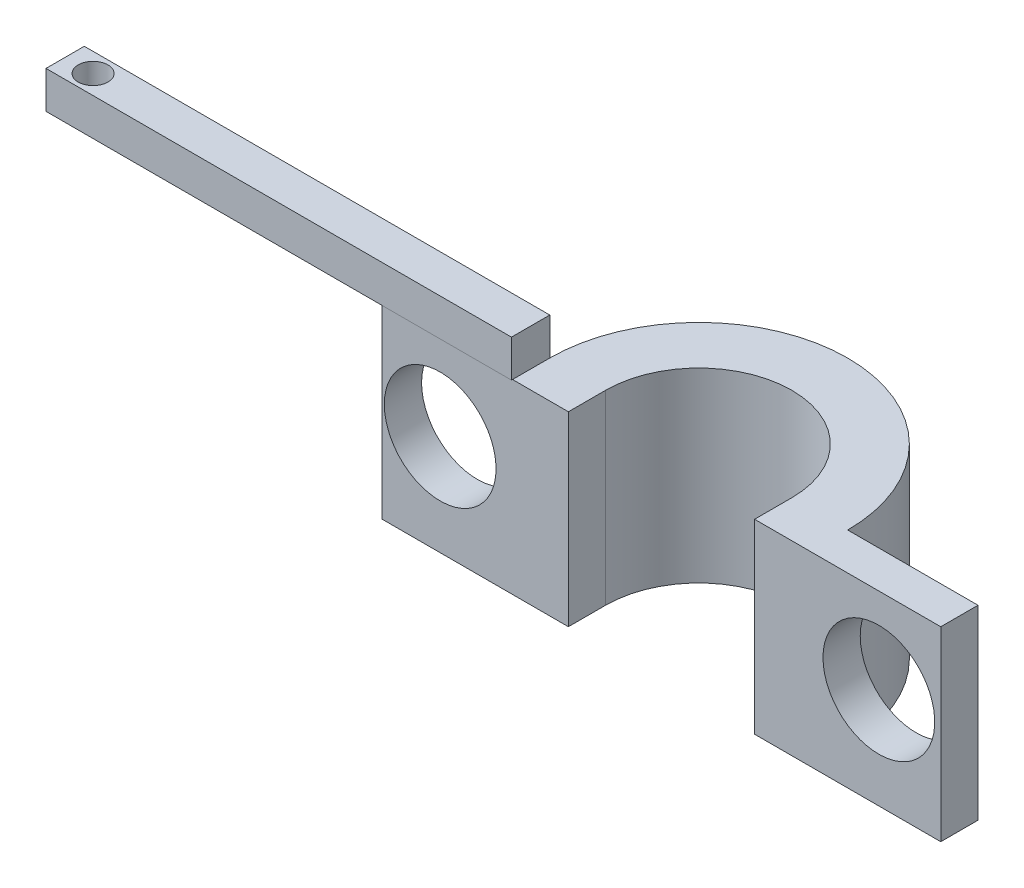
SolidWorks part; units mm, degrees
ref_plane "Front Plane" through (0, 0, 0) normal (0, 0, 1) x (1, 0, 0)
ref_plane "Top Plane" through (0, 0, 0) normal (0, 1, 0) x (1, 0, 0)
ref_plane "Right Plane" through (0, 0, 0) normal (1, 0, 0) x (0, 0, -1)
sketch "Sketch2" plane through (0, 0, 0) normal (0, 1, 0) x (1, 0, 0)
  circle A0 centre (0, 0) radius 5
extrude "Extrude-Thin1" add sketch "Sketch2" along normal blind 10 thin contours A0
sketch "Sketch3" plane through (0, 10, 0) normal (0, 1, 0) x (1, 0, 0)
  line L0 (-8, 0) -> (8, 0)
  circle A0 centre (0, 0) radius 8 construction
  arc A1 (-8, 0) -> (8, 0) centre (0, 0) ccw
extrude "Cut-Extrude1" cut sketch "Sketch3" against normal blind 10
sketch "Sketch4" plane through (0, 0, 0) normal (0, 0, 1) x (1, 0, 0)
  line L1 (5, 10) -> (15, 10)
  line L2 (5, 10) -> (5, 0)
  line L3 (5, 0) -> (15, 0)
  line L4 (15, 10) -> (15, 0)
  line L5 (-5, 10) -> (-15, 10)
  line L6 (-5, 10) -> (-5, 0)
  line L7 (-5, 0) -> (-15, 0)
  line L8 (-15, 10) -> (-15, 0)
  dimension "D1" = 10
  dimension "D2" = 10
extrude "Boss-Extrude1" add sketch "Sketch4" along normal blind 2
sketch "Sketch5" plane through (0, 0, 0) normal (0, 0, -1) x (-1, 0, 0)
  circle A0 centre (-11.6743, 5.4068) radius 3
  circle A1 centre (11.8859, 5.4068) radius 3
extrude "Cut-Extrude2" cut sketch "Sketch5" against normal blind 2
sketch "Sketch6" plane through (0, 10, 0) normal (0, 1, 0) x (1, 0, 0)
  line L1 (-8, 0) -> (-33, 0)
  line L2 (-8, 0) -> (-8, -2.0576)
  line L3 (-8, -2.0576) -> (-33, -2.0576)
  line L4 (-33, 0) -> (-33, -2.0576)
  dimension "D1" = 25
extrude "Boss-Extrude2" add sketch "Sketch6" along normal blind 2
sketch "Sketch7" plane through (0, 12, 0) normal (0, 1, 0) x (1, 0, 0)
  line L0 (-33, 0) -> (-33, -2.0576) construction
  circle A0 centre (-31.5, -1.0293) radius 0.8
  dimension "D1" = 1.5
extrude "Cut-Extrude3" cut sketch "Sketch7" against normal blind 2
